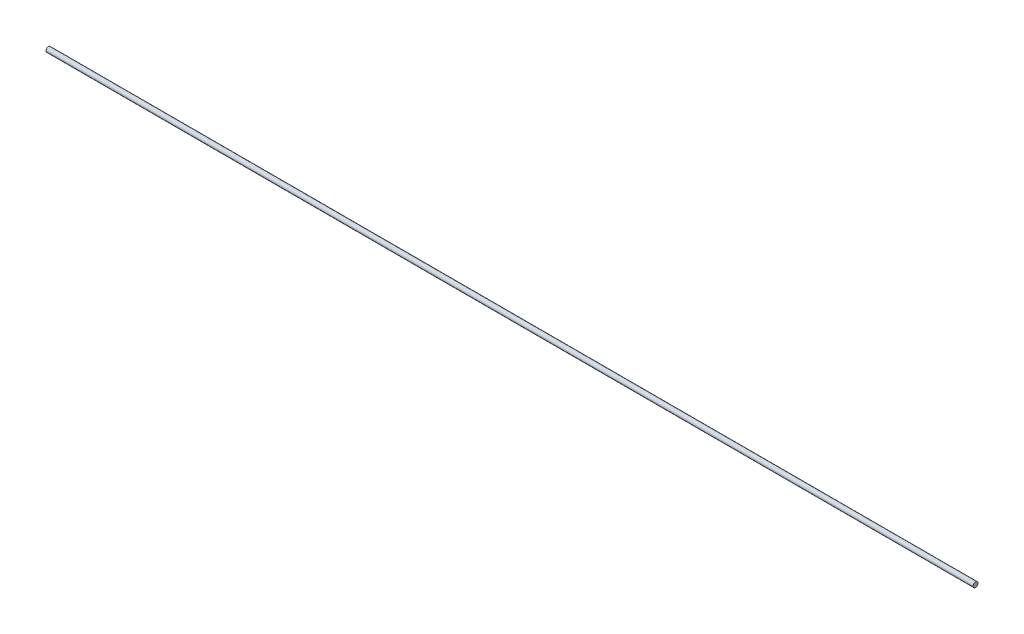
SolidWorks part; units mm, degrees
ref_plane "Front Plane" through (0, 0, 0) normal (0, 0, 1) x (1, 0, 0)
ref_plane "Top Plane" through (0, 0, 0) normal (0, 1, 0) x (1, 0, 0)
ref_plane "Right Plane" through (0, 0, 0) normal (1, 0, 0) x (0, 0, -1)
sketch "Sketch1" plane through (0, 0, 0) normal (1, 0, 0) x (0, 0, -1)
  circle A0 centre (0, 0) radius 1
  dimension "D1" = 2
extrude "Boss-Extrude1" add sketch "Sketch1" along normal blind 380
